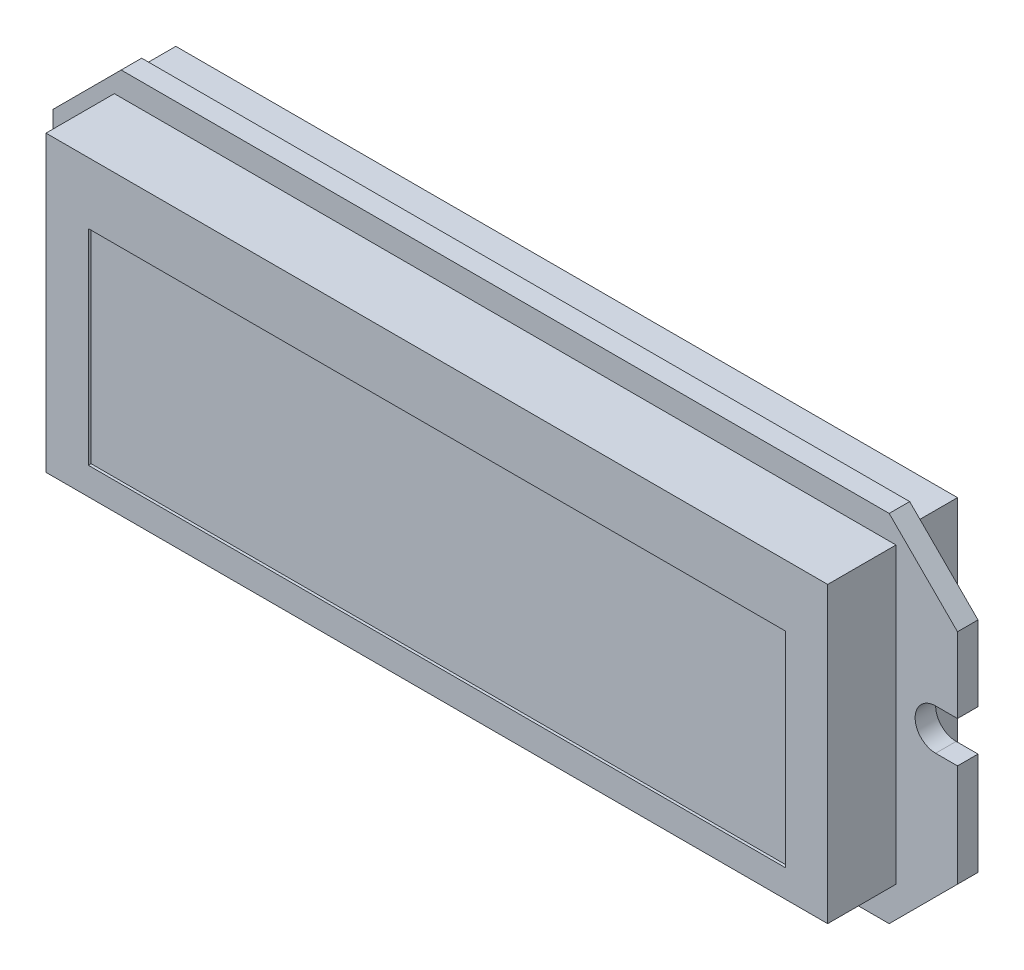
SolidWorks part; units mm, degrees
ref_plane "Спереди" through (0, 0, 0) normal (0, 0, 1) x (1, 0, 0)
ref_plane "Сверху" through (0, 0, 0) normal (0, 1, 0) x (1, 0, 0)
ref_plane "Справа" through (0, 0, 0) normal (1, 0, 0) x (0, 0, -1)
sketch "Эскиз1" plane through (0, 0, 0) normal (0, 0, 1) x (1, 0, 0)
  line L1 (33.1, 13) -> (-33.1, 13)
  line L2 (33.1, 13) -> (33.1, -13)
  line L3 (33.1, -13) -> (-33.1, -13)
  line L4 (-33.1, 13) -> (-33.1, -13)
  line L5 (33.1, 13) -> (-33.1, -13) construction
  line L6 (33.1, -13) -> (-33.1, 13) construction
  point P0 (0, 0)
  dimension "D1" = 26
  dimension "D2" = 66.2
extrude "Бобышка-Вытянуть1" add sketch "Эскиз1" against normal blind 1.5
sketch "Эскиз3" plane through (0, 0, 0) normal (0, 0, 1) x (1, 0, 0)
  line L0 (33.1, 13) -> (-33.1, 13) construction
  line L1 (-28.6, 11.25) -> (28.6, 11.25)
  line L2 (-28.6, 11.25) -> (-28.6, -10.25)
  line L3 (-28.6, -10.25) -> (28.6, -10.25)
  line L4 (28.6, 11.25) -> (28.6, -10.25)
  line L5 (-33.1, 13) -> (-33.1, -13) construction
  line L6 (33.1, -13) -> (33.1, 13) construction
  dimension "D1" = 1.75
  dimension "D2" = 21.5
  dimension "D3" = 57.2
  dimension "D4" = 4.5
  dimension "D5" = 4.5
extrude "Бобышка-Вытянуть2" add sketch "Эскиз3" along normal blind 5 contours L2 L3 L4 L1
chamfer "Фаска1" distance 5 angle 45 4 edges at (33.1, -13, -0.75) (33.1, 13, -0.75) (-33.1, -13, -0.75) (-33.1, 13, -0.75)
sketch "Эскиз5" plane through (0, 0, -1.5) normal (0, 0, -1) x (-1, 0, 0)
  line L0 (-33.1, 2.5) -> (-31.5, 2.5)
  line L1 (-33.1, -8) -> (-33.1, 8) construction
  line L2 (33.1, 8) -> (33.1, -8) construction
  line L3 (-28.1, 13) -> (28.1, 13) construction
  line L4 (-30, 2.5) -> (-30, -0.5) construction
  line L5 (-30, -0.5) -> (-31.5, -0.5) construction
  line L6 (-30, 1) -> (-31.5, 1) construction
  line L7 (-30, 2.5) -> (33.1, 2.5) construction
  line L8 (-31.5, -0.5) -> (-34.1, -0.5)
  line L9 (-34.1, -0.5) -> (-34.1, 2.5)
  line L10 (-34.1, 2.5) -> (-33.1, 2.5)
  line L11 (-30, 2.5) -> (-31.5, 2.5) construction
  line L12 (0, 0) -> (0, -3.7759) construction
  line L13 (30, 2.5) -> (31.5, 2.5) construction
  line L14 (30, 1) -> (31.5, 1) construction
  line L15 (30, -0.5) -> (31.5, -0.5) construction
  line L16 (30, 2.5) -> (30, -0.5) construction
  line L17 (34.1, 2.5) -> (33.1, 2.5)
  line L18 (34.1, -0.5) -> (34.1, 2.5)
  line L19 (31.5, -0.5) -> (34.1, -0.5)
  line L20 (33.1, 2.5) -> (31.5, 2.5)
  arc A0 (-31.5, -0.5) -> (-31.5, 2.5) centre (-31.5, 1) ccw
  arc A1 (31.5, -0.5) -> (31.5, 2.5) centre (31.5, 1) cw
  dimension "D1" = 10.5
  dimension "D2" = 30
  dimension "D3" = 3
  dimension "D4" = 3.1
  dimension "D5" = 1.5
  dimension "D6" = 1
extrude "Вырез-Вытянуть1" cut sketch "Эскиз5" against normal through all
sketch "Эскиз6" plane through (0, 0, 5) normal (0, 0, 1) x (1, 0, 0)
  line L0 (28.6, 11.25) -> (28.6, -10.25) construction
  line L1 (25.5, 6.75) -> (-25.5, 6.75)
  line L2 (25.5, 6.75) -> (25.5, -8.25)
  line L3 (25.5, -8.25) -> (-25.5, -8.25)
  line L4 (-25.5, 6.75) -> (-25.5, -8.25)
  line L5 (-28.6, -10.25) -> (28.6, -10.25) construction
  line L6 (-28.6, 11.25) -> (-28.6, -10.25) construction
  line L7 (-28.6, 11.25) -> (28.6, 11.25) construction
  dimension "D1" = 3.1
  dimension "D2" = 15
  dimension "D3" = 2
  dimension "D4" = 51
  dimension "D5" = 3.1
  dimension "D6" = 4.5
extrude "Вырез-Вытянуть2" cut sketch "Эскиз6" against normal blind 0.2
sketch "Эскиз7" plane through (0, 0, 0) normal (0, 0, 1) x (1, 0, 0)
  line L0 (-28.1, -13) -> (28.1, -13) construction
  line L1 (25.4, -13) -> (24.6, -13)
  line L2 (25.4, -13) -> (25.4, -11.85)
  line L3 (25.05, -11.5) -> (24.95, -11.5)
  line L4 (24.6, -13) -> (24.6, -11.85)
  line L5 (25.5, -8.25) -> (25.5, 6.75) construction
  line L6 (24.13, -13) -> (23.33, -13)
  line L7 (24.13, -13) -> (24.13, -11.85)
  line L8 (23.78, -11.5) -> (23.68, -11.5)
  line L9 (23.33, -13) -> (23.33, -11.85)
  line L10 (22.86, -13) -> (22.06, -13)
  line L11 (22.86, -13) -> (22.86, -11.85)
  line L12 (22.51, -11.5) -> (22.41, -11.5)
  line L13 (22.06, -13) -> (22.06, -11.85)
  line L14 (21.59, -13) -> (20.79, -13)
  line L15 (21.59, -13) -> (21.59, -11.85)
  line L16 (21.24, -11.5) -> (21.14, -11.5)
  line L17 (20.79, -13) -> (20.79, -11.85)
  line L18 (20.32, -13) -> (19.52, -13)
  line L19 (20.32, -13) -> (20.32, -11.85)
  line L20 (19.97, -11.5) -> (19.87, -11.5)
  line L21 (19.52, -13) -> (19.52, -11.85)
  line L22 (19.05, -13) -> (18.25, -13)
  line L23 (19.05, -13) -> (19.05, -11.85)
  line L24 (18.7, -11.5) -> (18.6, -11.5)
  line L25 (18.25, -13) -> (18.25, -11.85)
  line L26 (17.78, -13) -> (16.98, -13)
  line L27 (17.78, -13) -> (17.78, -11.85)
  line L28 (17.43, -11.5) -> (17.33, -11.5)
  line L29 (16.98, -13) -> (16.98, -11.85)
  line L30 (16.51, -13) -> (15.71, -13)
  line L31 (16.51, -13) -> (16.51, -11.85)
  line L32 (16.16, -11.5) -> (16.06, -11.5)
  line L33 (15.71, -13) -> (15.71, -11.85)
  line L34 (15.24, -13) -> (14.44, -13)
  line L35 (15.24, -13) -> (15.24, -11.85)
  line L36 (14.89, -11.5) -> (14.79, -11.5)
  line L37 (14.44, -13) -> (14.44, -11.85)
  line L38 (13.97, -13) -> (13.17, -13)
  line L39 (13.97, -13) -> (13.97, -11.85)
  line L40 (13.62, -11.5) -> (13.52, -11.5)
  line L41 (13.17, -13) -> (13.17, -11.85)
  line L42 (12.7, -13) -> (11.9, -13)
  line L43 (12.7, -13) -> (12.7, -11.85)
  line L44 (12.35, -11.5) -> (12.25, -11.5)
  line L45 (11.9, -13) -> (11.9, -11.85)
  line L46 (11.43, -13) -> (10.63, -13)
  line L47 (11.43, -13) -> (11.43, -11.85)
  line L48 (11.08, -11.5) -> (10.98, -11.5)
  line L49 (10.63, -13) -> (10.63, -11.85)
  line L50 (10.16, -13) -> (9.36, -13)
  line L51 (10.16, -13) -> (10.16, -11.85)
  line L52 (9.81, -11.5) -> (9.71, -11.5)
  line L53 (9.36, -13) -> (9.36, -11.85)
  line L54 (8.89, -13) -> (8.09, -13)
  line L55 (8.89, -13) -> (8.89, -11.85)
  line L56 (8.54, -11.5) -> (8.44, -11.5)
  line L57 (8.09, -13) -> (8.09, -11.85)
  arc A0 (25.4, -11.85) -> (25.05, -11.5) centre (25.05, -11.85) ccw
  arc A1 (24.95, -11.5) -> (24.6, -11.85) centre (24.95, -11.85) ccw
  arc A2 (24.13, -11.85) -> (23.78, -11.5) centre (23.78, -11.85) ccw
  arc A3 (23.68, -11.5) -> (23.33, -11.85) centre (23.68, -11.85) ccw
  arc A4 (22.86, -11.85) -> (22.51, -11.5) centre (22.51, -11.85) ccw
  arc A5 (22.41, -11.5) -> (22.06, -11.85) centre (22.41, -11.85) ccw
  arc A6 (21.59, -11.85) -> (21.24, -11.5) centre (21.24, -11.85) ccw
  arc A7 (21.14, -11.5) -> (20.79, -11.85) centre (21.14, -11.85) ccw
  arc A8 (20.32, -11.85) -> (19.97, -11.5) centre (19.97, -11.85) ccw
  arc A9 (19.87, -11.5) -> (19.52, -11.85) centre (19.87, -11.85) ccw
  arc A10 (19.05, -11.85) -> (18.7, -11.5) centre (18.7, -11.85) ccw
  arc A11 (18.6, -11.5) -> (18.25, -11.85) centre (18.6, -11.85) ccw
  arc A12 (17.78, -11.85) -> (17.43, -11.5) centre (17.43, -11.85) ccw
  arc A13 (17.33, -11.5) -> (16.98, -11.85) centre (17.33, -11.85) ccw
  arc A14 (16.51, -11.85) -> (16.16, -11.5) centre (16.16, -11.85) ccw
  arc A15 (16.06, -11.5) -> (15.71, -11.85) centre (16.06, -11.85) ccw
  arc A16 (15.24, -11.85) -> (14.89, -11.5) centre (14.89, -11.85) ccw
  arc A17 (14.79, -11.5) -> (14.44, -11.85) centre (14.79, -11.85) ccw
  arc A18 (13.97, -11.85) -> (13.62, -11.5) centre (13.62, -11.85) ccw
  arc A19 (13.52, -11.5) -> (13.17, -11.85) centre (13.52, -11.85) ccw
  arc A20 (12.7, -11.85) -> (12.35, -11.5) centre (12.35, -11.85) ccw
  arc A21 (12.25, -11.5) -> (11.9, -11.85) centre (12.25, -11.85) ccw
  arc A22 (11.43, -11.85) -> (11.08, -11.5) centre (11.08, -11.85) ccw
  arc A23 (10.98, -11.5) -> (10.63, -11.85) centre (10.98, -11.85) ccw
  arc A24 (10.16, -11.85) -> (9.81, -11.5) centre (9.81, -11.85) ccw
  arc A25 (9.71, -11.5) -> (9.36, -11.85) centre (9.71, -11.85) ccw
  arc A26 (8.89, -11.85) -> (8.54, -11.5) centre (8.54, -11.85) ccw
  arc A27 (8.44, -11.5) -> (8.09, -11.85) centre (8.44, -11.85) ccw
  dimension "D4" = 0.35
  dimension "D1" = 0.8
  dimension "D2" = 1.5
  dimension "D3" = 0.1
  dimension "D6" = 17.31
  dimension "D5" = 14
extrude "Бобышка-Вытянуть3" add sketch "Эскиз7" along normal blind 0.05 and the other way blind 1.6
sketch "Эскиз9" plane through (0, 0, -1.5) normal (0, 0, -1) x (-1, 0, 0)
  line L0 (-33.1, 2.5) -> (-33.1, 8) construction
  line L1 (-28.6, 12) -> (28.6, 12)
  line L2 (-28.6, 12) -> (-28.6, -10)
  line L3 (-28.6, -10) -> (28.6, -10)
  line L4 (28.6, 12) -> (28.6, -10)
  line L5 (33.1, 8) -> (33.1, 2.5) construction
  line L6 (-28.1, 13) -> (28.1, 13) construction
  line L7 (28.1, -13) -> (-8.09, -13) construction
  dimension "D1" = 4.5
  dimension "D2" = 4.5
  dimension "D3" = 1
  dimension "D4" = 3
extrude "Бобышка-Вытянуть4" add sketch "Эскиз9" along normal blind 3
